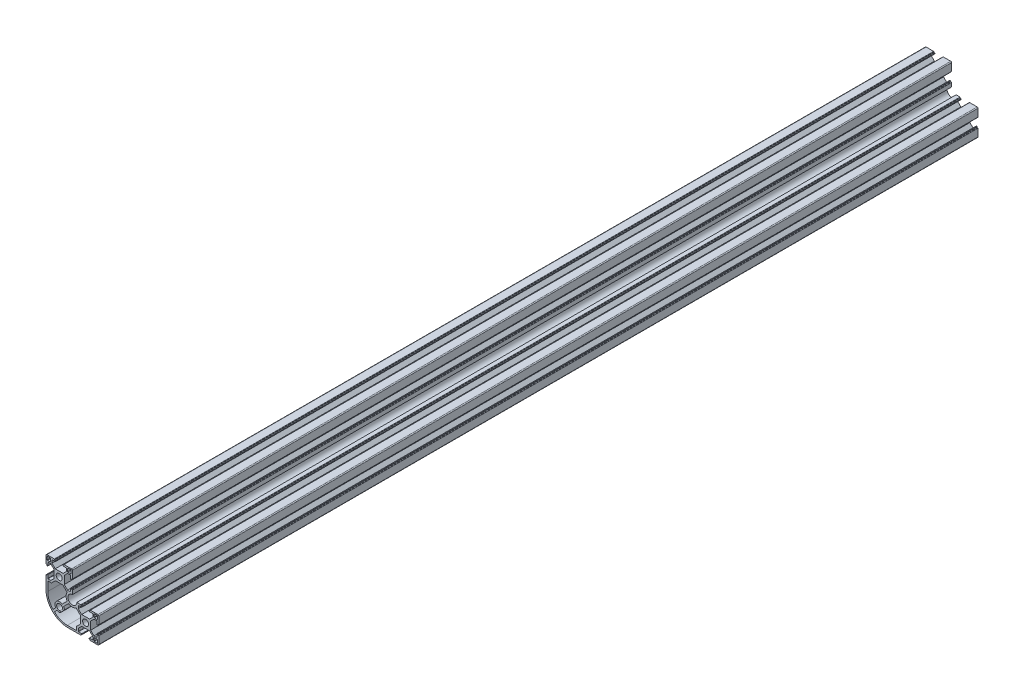
SolidWorks part; units mm, degrees
material "6063 T5"
ref_plane "Спереди" through (0, 0, 0) normal (0, 0, 1) x (1, 0, 0)
ref_plane "Сверху" through (0, 0, 0) normal (0, 1, 0) x (1, 0, 0)
ref_plane "Справа" through (0, 0, 0) normal (1, 0, 0) x (0, 0, -1)
sketch "Эскиз1" plane through (0, 0, 0) normal (0, 0, 1) x (1, 0, 0)
  line L0 (-14.9891, 50.0924) -> (45.0109, 50.0924) construction
  line L1 (0, 30) -> (0, 0) construction
  line L2 (0, 0) -> (30, 0) construction
  line L3 (-15, 38.25) -> (-15, 44)
  line L4 (-14, 45) -> (-8.25, 45)
  line L7 (-13.2, 43.7) -> (-10.2, 43.7)
  line L8 (-13.7, 43.2) -> (-13.7, 40.2)
  line L9 (-13.2, 39.7) -> (-10.2, 39.7)
  line L10 (-9.7, 43.2) -> (-9.7, 40.2)
  line L11 (14, 45) -> (8.25, 45)
  line L12 (15, 38.25) -> (15, 44)
  line L13 (13.2, 43.7) -> (10.2, 43.7)
  line L14 (13.7, 43.2) -> (13.7, 40.2)
  line L15 (13.2, 39.7) -> (10.2, 39.7)
  line L16 (9.7, 43.2) -> (9.7, 40.2)
  line L17 (0, 15) -> (-23.8455, 15) construction
  line L18 (-15, 21.75) -> (-15, 10)
  line L19 (15, 20.1) -> (15, 21.75)
  line L20 (20.1, 15) -> (21.75, 15)
  line L21 (10, -15) -> (21.75, -15)
  line L26 (43.7, 13.2) -> (43.7, 10.2)
  line L27 (43.2, 13.7) -> (40.2, 13.7)
  line L28 (15, 0) -> (15, -23.5964) construction
  line L29 (39.7, 13.2) -> (39.7, 10.2)
  line L30 (43.2, 9.7) -> (40.2, 9.7)
  line L39 (45, 14) -> (45, 8.25)
  line L40 (38.25, 15) -> (44, 15)
  line L51 (0, 0) -> (30, 30) construction
  line L62 (39.7, -13.2) -> (39.7, -10.2)
  line L63 (43.2, -9.7) -> (40.2, -9.7)
  line L64 (43.7, -13.2) -> (43.7, -10.2)
  line L65 (43.2, -13.7) -> (40.2, -13.7)
  line L66 (45, -14) -> (45, -8.25)
  line L67 (38.25, -15) -> (44, -15)
  line L68 (-15.0534, 53.8786) -> (44.9466, 53.8786) construction
  line L69 (-13, 19.75) -> (-13, 9.25)
  line L70 (-6.9388, -5.3831) -> (-4.0161, -2.4605)
  line L71 (3.4605, 5.0161) -> (9.1908, 10.7464)
  line L72 (9.2023, 19.2693) -> (4.2716, 24.2)
  line L73 (4.2716, 24.2) -> (-4.2716, 24.2)
  line L74 (-4.2716, 24.2) -> (-8.7216, 19.75)
  line L75 (-8.7216, 19.75) -> (-13, 19.75)
  line L76 (19.75, -13) -> (9.25, -13)
  line L77 (19.75, -8.7216) -> (19.75, -13)
  line L78 (24.2, -4.2716) -> (19.75, -8.7216)
  line L79 (24.2, 4.2716) -> (24.2, -4.2716)
  line L80 (19.2693, 9.2023) -> (24.2, 4.2716)
  line L81 (5.0161, 3.4605) -> (10.7464, 9.1908)
  line L82 (-5.3831, -6.9388) -> (-2.4605, -4.0161)
  arc A0 (-15, 44) -> (-14, 45) centre (-14, 44) cw
  arc A1 (-13.7, 40.2) -> (-13.2, 39.7) centre (-13.2, 40.2) ccw
  arc A2 (-10.2, 39.7) -> (-9.7, 40.2) centre (-10.2, 40.2) ccw
  arc A3 (-10.2, 43.7) -> (-9.7, 43.2) centre (-10.2, 43.2) cw
  arc A4 (-13.2, 43.7) -> (-13.7, 43.2) centre (-13.2, 43.2) ccw
  arc A5 (15, 44) -> (14, 45) centre (14, 44) ccw
  arc A6 (10.2, 43.7) -> (9.7, 43.2) centre (10.2, 43.2) ccw
  arc A7 (13.2, 43.7) -> (13.7, 43.2) centre (13.2, 43.2) cw
  arc A8 (13.7, 40.2) -> (13.2, 39.7) centre (13.2, 40.2) cw
  arc A9 (10.2, 39.7) -> (9.7, 40.2) centre (10.2, 40.2) cw
  arc A14 (-15, 10) -> (10, -15) centre (10, 10) ccw
  arc A15 (43.7, 13.2) -> (43.2, 13.7) centre (43.2, 13.2) ccw
  arc A24 (40.2, 13.7) -> (39.7, 13.2) centre (40.2, 13.2) ccw
  circle A31 centre (0, 30) radius 3.4
  circle A32 centre (30, 0) radius 3.4
  arc A33 (39.7, 10.2) -> (40.2, 9.7) centre (40.2, 10.2) ccw
  arc A34 (43.7, 10.2) -> (43.2, 9.7) centre (43.2, 10.2) cw
  arc A35 (44, 15) -> (45, 14) centre (44, 14) cw
  arc A36 (39.7, -10.2) -> (40.2, -9.7) centre (40.2, -10.2) cw
  arc A37 (43.7, -10.2) -> (43.2, -9.7) centre (43.2, -10.2) ccw
  arc A38 (40.2, -13.7) -> (39.7, -13.2) centre (40.2, -13.2) cw
  arc A39 (43.7, -13.2) -> (43.2, -13.7) centre (43.2, -13.2) cw
  arc A40 (44, -15) -> (45, -14) centre (44, -14) ccw
  arc A41 (15, 20.1) -> (20.1, 15) centre (15, 15) ccw
  arc A42 (-13, 9.25) -> (-6.9388, -5.3831) centre (7.6944, 9.25) ccw
  arc A46 (9.2023, 19.2693) -> (9.1908, 10.7464) centre (15, 15) ccw
  arc A47 (-4.0161, -2.4605) -> (3.4605, 5.0161) centre (0.5, 0.5) cw
  arc A48 (19.2693, 9.2023) -> (10.7464, 9.1908) centre (15, 15) cw
  arc A50 (9.25, -13) -> (-5.3831, -6.9388) centre (9.25, 7.6944) cw
  arc A51 (-2.4605, -4.0161) -> (0.5, -4.9) centre (0.5, 0.5) ccw
  arc A52 (0.5, -4.9) -> (0.5, -2.9) centre (0.5, -3.9) ccw
  arc A53 (0.5, -2.9) -> (3.9, 0.5) centre (0.5, 0.5) cw
  arc A54 (5.0161, 3.4605) -> (5.9, 0.5) centre (0.5, 0.5) cw
  arc A55 (5.9, 0.5) -> (3.9, 0.5) centre (4.9, 0.5) cw
  point P2 (0, 30)
  point P7 (30, 0)
  point P22 (-9.7, 43.7)
  point P25 (-13.7, 43.7)
  line B0 (-15, 38.25) -> (-15, 35.5)
  line B1 (-14.7, 35.2) -> (-14.3, 35.2)
  line B2 (-14, 34.9) -> (-14, 34.4)
  line B3 (-13.7, 34.1) -> (-13.3, 34.1)
  line B4 (-13, 34.4) -> (-13, 37.95)
  line B5 (-12.7, 38.25) -> (-9.55, 38.25)
  line B6 (-9.55, 38.25) -> (-5.8, 34.5)
  line B7 (-5.8, 30) -> (-15, 30) construction
  line B8 (-5.8, 25.5) -> (-5.8, 34.5)
  line B9 (-9.55, 21.75) -> (-5.8, 25.5)
  line B10 (-12.7, 21.75) -> (-9.55, 21.75)
  line B11 (-13, 25.6) -> (-13, 22.05)
  line B12 (-13.7, 25.9) -> (-13.3, 25.9)
  line B13 (-14, 25.1) -> (-14, 25.6)
  line B14 (-14.7, 24.8) -> (-14.3, 24.8)
  line B15 (-15, 21.75) -> (-15, 24.5)
  arc B16 (-13, 37.95) -> (-12.7, 38.25) centre (-12.7, 37.95) cw
  arc B17 (-13.3, 34.1) -> (-13, 34.4) centre (-13.3, 34.4) ccw
  arc B18 (-14, 34.4) -> (-13.7, 34.1) centre (-13.7, 34.4) ccw
  arc B19 (-14.3, 35.2) -> (-14, 34.9) centre (-14.3, 34.9) cw
  arc B20 (-15, 35.5) -> (-14.7, 35.2) centre (-14.7, 35.5) ccw
  arc B21 (-15, 24.5) -> (-14.7, 24.8) centre (-14.7, 24.5) cw
  arc B22 (-14.3, 24.8) -> (-14, 25.1) centre (-14.3, 25.1) ccw
  arc B23 (-14, 25.6) -> (-13.7, 25.9) centre (-13.7, 25.6) cw
  arc B24 (-13.3, 25.9) -> (-13, 25.6) centre (-13.3, 25.6) cw
  arc B25 (-13, 22.05) -> (-12.7, 21.75) centre (-12.7, 22.05) ccw
  line B26 (8.25, 45) -> (5.5, 45)
  line B27 (5.2, 44.7) -> (5.2, 44.3)
  line B28 (4.9, 44) -> (4.4, 44)
  line B29 (4.1, 43.7) -> (4.1, 43.3)
  line B30 (4.4, 43) -> (7.95, 43)
  line B31 (8.25, 42.7) -> (8.25, 39.55)
  line B32 (8.25, 39.55) -> (4.5, 35.8)
  line B33 (0, 35.8) -> (0, 45) construction
  line B34 (-4.5, 35.8) -> (4.5, 35.8)
  line B35 (-8.25, 39.55) -> (-4.5, 35.8)
  line B36 (-8.25, 42.7) -> (-8.25, 39.55)
  line B37 (-4.4, 43) -> (-7.95, 43)
  line B38 (-4.1, 43.7) -> (-4.1, 43.3)
  line B39 (-4.9, 44) -> (-4.4, 44)
  line B40 (-5.2, 44.7) -> (-5.2, 44.3)
  line B41 (-8.25, 45) -> (-5.5, 45)
  arc B42 (7.95, 43) -> (8.25, 42.7) centre (7.95, 42.7) cw
  arc B43 (4.1, 43.3) -> (4.4, 43) centre (4.4, 43.3) ccw
  arc B44 (4.4, 44) -> (4.1, 43.7) centre (4.4, 43.7) ccw
  arc B45 (5.2, 44.3) -> (4.9, 44) centre (4.9, 44.3) cw
  arc B46 (5.5, 45) -> (5.2, 44.7) centre (5.5, 44.7) ccw
  arc B47 (-5.5, 45) -> (-5.2, 44.7) centre (-5.5, 44.7) cw
  arc B48 (-5.2, 44.3) -> (-4.9, 44) centre (-4.9, 44.3) ccw
  arc B49 (-4.4, 44) -> (-4.1, 43.7) centre (-4.4, 43.7) cw
  arc B50 (-4.1, 43.3) -> (-4.4, 43) centre (-4.4, 43.3) cw
  arc B51 (-7.95, 43) -> (-8.25, 42.7) centre (-7.95, 42.7) ccw
  line B52 (15, 21.75) -> (15, 24.5)
  line B53 (14.7, 24.8) -> (14.3, 24.8)
  line B54 (14, 25.1) -> (14, 25.6)
  line B55 (13.7, 25.9) -> (13.3, 25.9)
  line B56 (13, 25.6) -> (13, 22.05)
  line B57 (12.7, 21.75) -> (9.55, 21.75)
  line B58 (9.55, 21.75) -> (5.8, 25.5)
  line B59 (5.8, 30) -> (15, 30) construction
  line B60 (5.8, 34.5) -> (5.8, 25.5)
  line B61 (9.55, 38.25) -> (5.8, 34.5)
  line B62 (12.7, 38.25) -> (9.55, 38.25)
  line B63 (13, 34.4) -> (13, 37.95)
  line B64 (13.7, 34.1) -> (13.3, 34.1)
  line B65 (14, 34.9) -> (14, 34.4)
  line B66 (14.7, 35.2) -> (14.3, 35.2)
  line B67 (15, 38.25) -> (15, 35.5)
  arc B68 (13, 22.05) -> (12.7, 21.75) centre (12.7, 22.05) cw
  arc B69 (13.3, 25.9) -> (13, 25.6) centre (13.3, 25.6) ccw
  arc B70 (14, 25.6) -> (13.7, 25.9) centre (13.7, 25.6) ccw
  arc B71 (14.3, 24.8) -> (14, 25.1) centre (14.3, 25.1) cw
  arc B72 (15, 24.5) -> (14.7, 24.8) centre (14.7, 24.5) ccw
  arc B73 (15, 35.5) -> (14.7, 35.2) centre (14.7, 35.5) cw
  arc B74 (14.3, 35.2) -> (14, 34.9) centre (14.3, 34.9) ccw
  arc B75 (14, 34.4) -> (13.7, 34.1) centre (13.7, 34.4) cw
  arc B76 (13.3, 34.1) -> (13, 34.4) centre (13.3, 34.4) cw
  arc B77 (13, 37.95) -> (12.7, 38.25) centre (12.7, 37.95) ccw
  line B78 (38.25, 15) -> (35.5, 15)
  line B79 (35.2, 14.7) -> (35.2, 14.3)
  line B80 (34.9, 14) -> (34.4, 14)
  line B81 (34.1, 13.7) -> (34.1, 13.3)
  line B82 (34.4, 13) -> (37.95, 13)
  line B83 (38.25, 12.7) -> (38.25, 9.55)
  line B84 (38.25, 9.55) -> (34.5, 5.8)
  line B85 (30, 5.8) -> (30, 15) construction
  line B86 (25.5, 5.8) -> (34.5, 5.8)
  line B87 (21.75, 9.55) -> (25.5, 5.8)
  line B88 (21.75, 12.7) -> (21.75, 9.55)
  line B89 (25.6, 13) -> (22.05, 13)
  line B90 (25.9, 13.7) -> (25.9, 13.3)
  line B91 (25.1, 14) -> (25.6, 14)
  line B92 (24.8, 14.7) -> (24.8, 14.3)
  line B93 (21.75, 15) -> (24.5, 15)
  arc B94 (37.95, 13) -> (38.25, 12.7) centre (37.95, 12.7) cw
  arc B95 (34.1, 13.3) -> (34.4, 13) centre (34.4, 13.3) ccw
  arc B96 (34.4, 14) -> (34.1, 13.7) centre (34.4, 13.7) ccw
  arc B97 (35.2, 14.3) -> (34.9, 14) centre (34.9, 14.3) cw
  arc B98 (35.5, 15) -> (35.2, 14.7) centre (35.5, 14.7) ccw
  arc B99 (24.5, 15) -> (24.8, 14.7) centre (24.5, 14.7) cw
  arc B100 (24.8, 14.3) -> (25.1, 14) centre (25.1, 14.3) ccw
  arc B101 (25.6, 14) -> (25.9, 13.7) centre (25.6, 13.7) cw
  arc B102 (25.9, 13.3) -> (25.6, 13) centre (25.6, 13.3) cw
  arc B103 (22.05, 13) -> (21.75, 12.7) centre (22.05, 12.7) ccw
  line B104 (45, -8.25) -> (45, -5.5)
  line B105 (44.7, -5.2) -> (44.3, -5.2)
  line B106 (44, -4.9) -> (44, -4.4)
  line B107 (43.7, -4.1) -> (43.3, -4.1)
  line B108 (43, -4.4) -> (43, -7.95)
  line B109 (42.7, -8.25) -> (39.55, -8.25)
  line B110 (39.55, -8.25) -> (35.8, -4.5)
  line B111 (35.8, 0) -> (45, 0) construction
  line B112 (35.8, 4.5) -> (35.8, -4.5)
  line B113 (39.55, 8.25) -> (35.8, 4.5)
  line B114 (42.7, 8.25) -> (39.55, 8.25)
  line B115 (43, 4.4) -> (43, 7.95)
  line B116 (43.7, 4.1) -> (43.3, 4.1)
  line B117 (44, 4.9) -> (44, 4.4)
  line B118 (44.7, 5.2) -> (44.3, 5.2)
  line B119 (45, 8.25) -> (45, 5.5)
  arc B120 (43, -7.95) -> (42.7, -8.25) centre (42.7, -7.95) cw
  arc B121 (43.3, -4.1) -> (43, -4.4) centre (43.3, -4.4) ccw
  arc B122 (44, -4.4) -> (43.7, -4.1) centre (43.7, -4.4) ccw
  arc B123 (44.3, -5.2) -> (44, -4.9) centre (44.3, -4.9) cw
  arc B124 (45, -5.5) -> (44.7, -5.2) centre (44.7, -5.5) ccw
  arc B125 (45, 5.5) -> (44.7, 5.2) centre (44.7, 5.5) cw
  arc B126 (44.3, 5.2) -> (44, 4.9) centre (44.3, 4.9) ccw
  arc B127 (44, 4.4) -> (43.7, 4.1) centre (43.7, 4.4) cw
  arc B128 (43.3, 4.1) -> (43, 4.4) centre (43.3, 4.4) cw
  arc B129 (43, 7.95) -> (42.7, 8.25) centre (42.7, 7.95) ccw
  line B130 (21.75, -15) -> (24.5, -15)
  line B131 (24.8, -14.7) -> (24.8, -14.3)
  line B132 (25.1, -14) -> (25.6, -14)
  line B133 (25.9, -13.7) -> (25.9, -13.3)
  line B134 (25.6, -13) -> (22.05, -13)
  line B135 (21.75, -12.7) -> (21.75, -9.55)
  line B136 (21.75, -9.55) -> (25.5, -5.8)
  line B137 (30, -5.8) -> (30, -15) construction
  line B138 (34.5, -5.8) -> (25.5, -5.8)
  line B139 (38.25, -9.55) -> (34.5, -5.8)
  line B140 (38.25, -12.7) -> (38.25, -9.55)
  line B141 (34.4, -13) -> (37.95, -13)
  line B142 (34.1, -13.7) -> (34.1, -13.3)
  line B143 (34.9, -14) -> (34.4, -14)
  line B144 (35.2, -14.7) -> (35.2, -14.3)
  line B145 (38.25, -15) -> (35.5, -15)
  arc B146 (22.05, -13) -> (21.75, -12.7) centre (22.05, -12.7) cw
  arc B147 (25.9, -13.3) -> (25.6, -13) centre (25.6, -13.3) ccw
  arc B148 (25.6, -14) -> (25.9, -13.7) centre (25.6, -13.7) ccw
  arc B149 (24.8, -14.3) -> (25.1, -14) centre (25.1, -14.3) cw
  arc B150 (24.5, -15) -> (24.8, -14.7) centre (24.5, -14.7) ccw
  arc B151 (35.5, -15) -> (35.2, -14.7) centre (35.5, -14.7) cw
  arc B152 (35.2, -14.3) -> (34.9, -14) centre (34.9, -14.3) ccw
  arc B153 (34.4, -14) -> (34.1, -13.7) centre (34.4, -13.7) cw
  arc B154 (34.1, -13.3) -> (34.4, -13) centre (34.4, -13.3) cw
  arc B155 (37.95, -13) -> (38.25, -12.7) centre (37.95, -12.7) ccw
  dimension "D3" = 15
  dimension "D6" = 1
  dimension "D10" = 0.5
  dimension "D15" = 2
  dimension "D18" = 6.8
  dimension "D19" = 6.8
  dimension "D4" = 25
  dimension "D12" = 5.1
  dimension "D23" = 7.2
  dimension "D24" = 5.4
  dimension "D25" = 0.5
  dimension "D26" = 3.4
  dimension "D1" = 60
  dimension "D2" = 30
  dimension "D5" = 15
  dimension "D7" = 1.3
  dimension "D8" = 1.3
  dimension "D9" = 4
  dimension "D11" = 60
  dimension "D13" = 2
  dimension "D14" = 2
  dimension "D16" = 45
  dimension "D17" = 5.8
  dimension "D20" = 2
  dimension "D21" = 1.1
  dimension "D22" = 10.5
  dimension "D27" = 0.5
  dimension "D28" = 0.5
sketch_block_instance "8B(16,5P)-1"
sketch_block "8B(16,5P)" parameters "D7"=0.3, "D1"=16.5, "D2"=2, "D3"=9, "D4"=9.2, "D5"=45, "D6"=10.4, "D8"=0.4, "D9"=0.5
sketch_block_instance "8B(16,5P)-3"
sketch_block_instance "8B(16,5P)-4"
sketch_block_instance "8B(16,5P)-8"
sketch_block_instance "8B(16,5P)-9"
sketch_block_instance "8B(16,5P)-10"
extrude "Бобышка-Вытянуть1" add sketch "Эскиз1" along normal blind 1000
